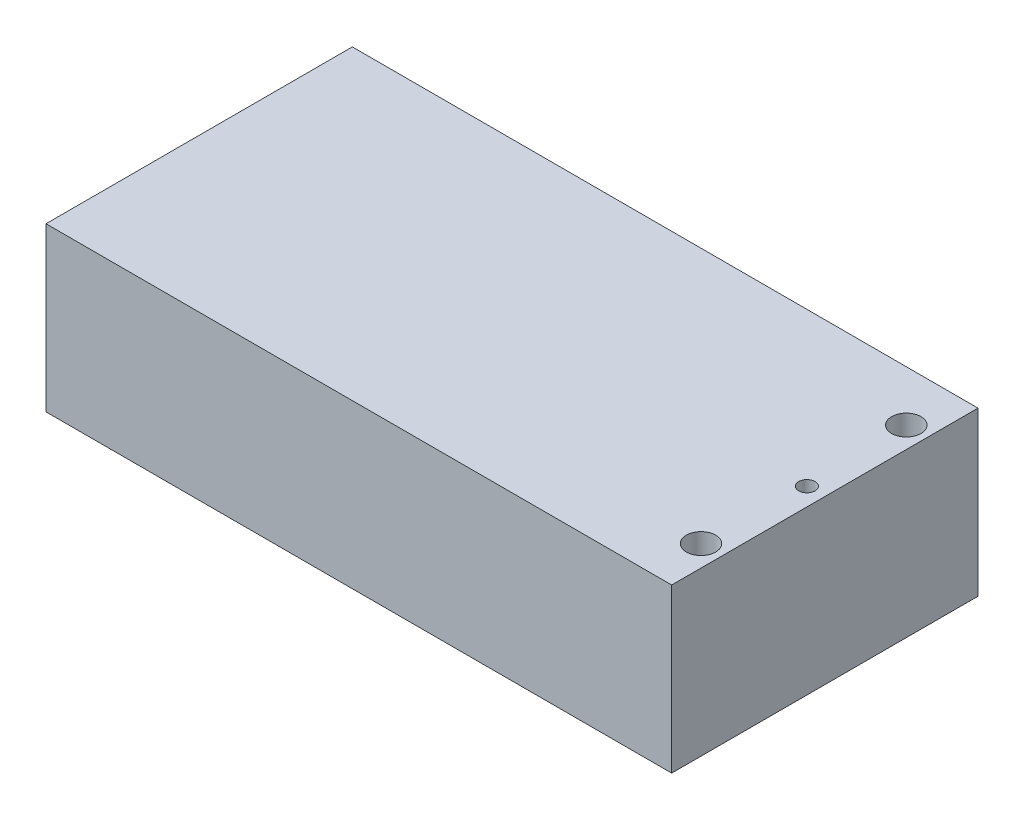
SolidWorks part; units mm, degrees
ref_plane "Ön Düzlem" through (0, 0, 0) normal (0, 0, 1) x (1, 0, 0)
ref_plane "Üst Düzlem" through (0, 0, 0) normal (0, 1, 0) x (1, 0, 0)
ref_plane "Sağ Düzlem" through (0, 0, 0) normal (1, 0, 0) x (0, 0, -1)
sketch "Sketch1" plane through (0, 0, 0) normal (0, 1, 0) x (1, 0, 0)
  line L1 (-48, -23.5) -> (48, -23.5)
  line L2 (-48, -23.5) -> (-48, 23.5)
  line L3 (-48, 23.5) -> (48, 23.5)
  line L4 (48, -23.5) -> (48, 23.5)
  line L5 (-48, -23.5) -> (48, 23.5) construction
  line L6 (-48, 23.5) -> (48, -23.5) construction
  point P0 (0, 0)
  dimension "D1" = 96
  dimension "D2" = 47
extrude "Boss-Extrude1" add sketch "Sketch1" along normal blind 25
sketch "Sketch2" plane through (0, 25, 0) normal (0, 1, 0) x (1, 0, 0)
  line L0 (44.75, 18) -> (44.75, 23.5) construction
  line L1 (48, 23.5) -> (-48, 23.5) construction
  line L2 (47, 15.75) -> (48, 15.75) construction
  line L3 (48, -23.5) -> (48, 23.5) construction
  line L5 (46.5, 0) -> (48, 0) construction
  line L6 (44.75, -18) -> (44.75, -23.5) construction
  line L8 (-48, -23.5) -> (48, -23.5) construction
  circle A0 centre (44.75, 15.75) radius 2.25
  circle A1 centre (44.75, -15.75) radius 2.25
  circle A2 centre (45.25, 0) radius 1.25
  dimension "D1" = 4.5
  dimension "D5" = 2.5
  dimension "D2" = 5.5
  dimension "D3" = 1
  dimension "D6" = 1.5
  dimension "D7" = 0.5
extrude "Cut-Extrude1" cut sketch "Sketch2" against normal blind 10
